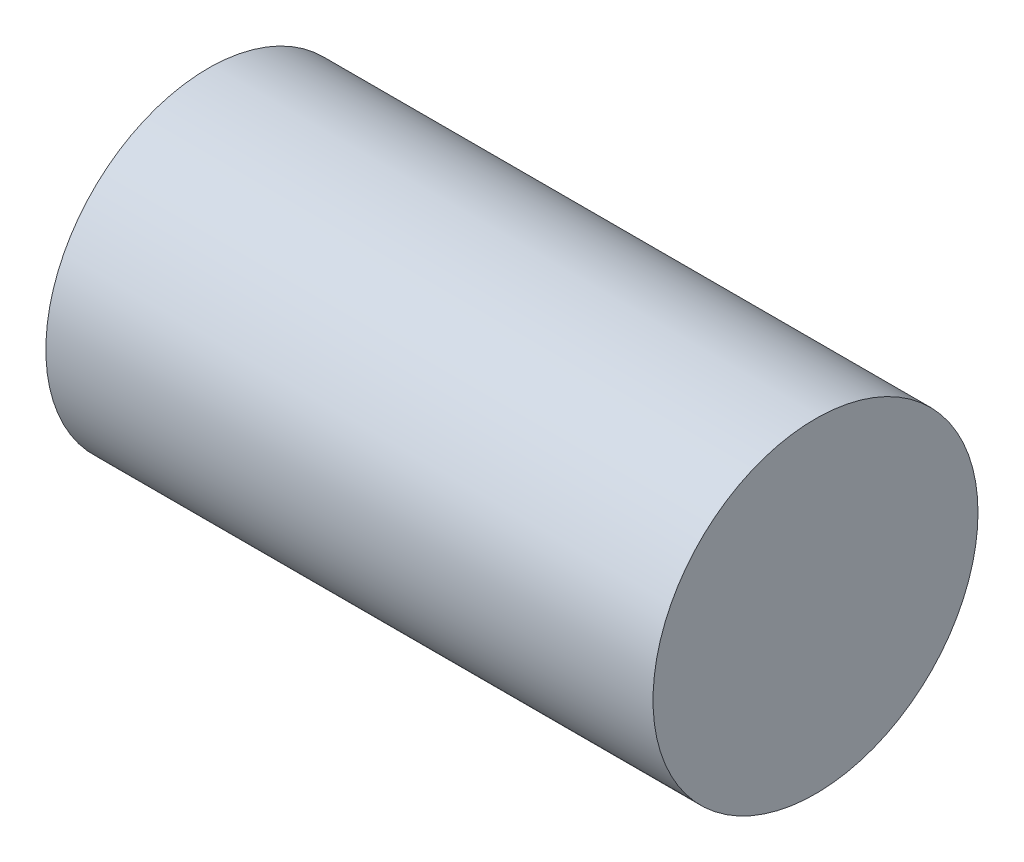
SolidWorks part; units mm, degrees
ref_plane "Front Plane" through (0, 0, 0) normal (0, 0, 1) x (1, 0, 0)
ref_plane "Top Plane" through (0, 0, 0) normal (0, 1, 0) x (1, 0, 0)
ref_plane "Right Plane" through (0, 0, 0) normal (1, 0, 0) x (0, 0, -1)
sketch "Sketch1" plane through (0, 0, 0) normal (1, 0, 0) x (0, 0, -1)
  circle A0 centre (0, 0) radius 3.0861
  dimension "D1" = 6.1722
extrude "Boss-Extrude1" add sketch "Sketch1" along normal mid plane 11.5316
